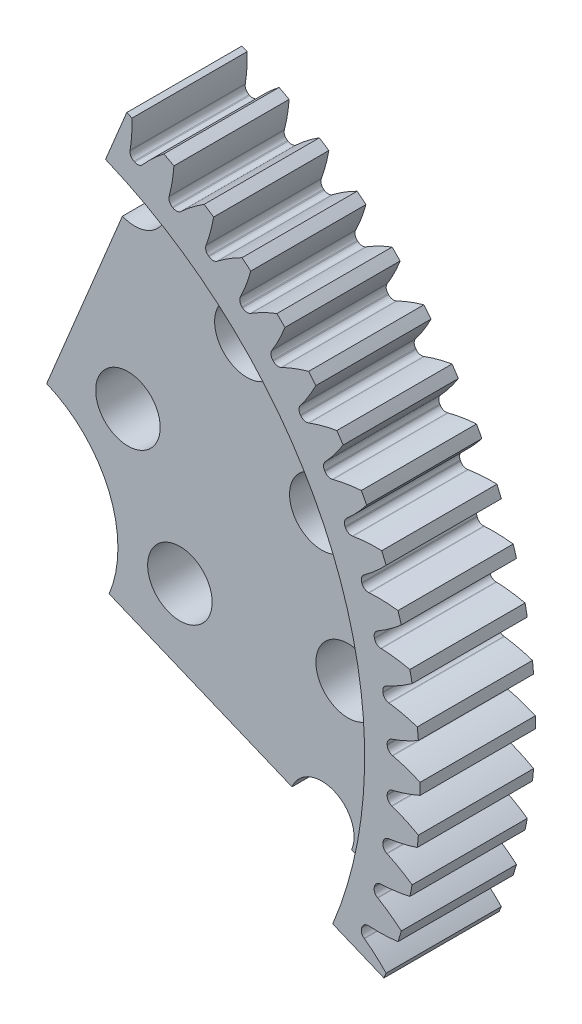
SolidWorks part; units mm, degrees
ref_plane "前视基准面" through (0, 0, 0) normal (0, 0, 1) x (1, 0, 0)
ref_plane "上视基准面" through (0, 0, 0) normal (0, 1, 0) x (1, 0, 0)
ref_plane "右视基准面" through (0, 0, 0) normal (1, 0, 0) x (0, 0, -1)
ref_plane "基准面4" through (0, 0, 0) normal (-0.3827, -0.9239, 0) x (0.9239, -0.3827, 0)
sketch "草图1" plane through (0, 0, 0) normal (-0.3827, -0.9239, 0) x (0.9239, -0.3827, 0)
  line L0 (0, 6.35) -> (0, 0)
  line L1 (0, 0) -> (26.1938, 0)
  line L2 (26.1938, 0) -> (26.1938, 6.35)
  line L3 (26.1938, 6.35) -> (0, 6.35)
  line L4 (0, 6.35) -> (0, 0) construction
revolve "旋转1" add sketch "草图1" angle 90 about L4
sketch "草图2" plane through (0, 0, 0) normal (0, 0, -1) x (-1, 0, 0)
  line L0 (-23.1251, -8.6864) -> (-22.8789, -8.5028)
  line L1 (-23.0797, -7.9415) -> (-23.3866, -7.9557)
  arc A0 (-24.9732, -7.9027) -> (-24.318, -9.7339) centre (0, 0) ccw
  arc A1 (-23.1251, -8.6864) -> (-24.318, -9.7339) centre (-18.0521, -15.6661) ccw
  arc A2 (-22.8789, -8.5028) -> (-23.0797, -7.9415) centre (0, 0) cw
  arc A3 (-24.9732, -7.9027) -> (-23.3866, -7.9557) centre (-23.8956, 0.5798) ccw
extrude "切除-拉伸1" cut sketch "草图2" against normal through all
sketch "草图3" plane through (0, 0, 0) normal (0, 0, -1) x (-1, 0, 0)
  line L0 (-23.8652, -6.3779) -> (-23.6022, -6.2193)
  line L1 (-23.747, -5.641) -> (-24.0537, -5.6251)
  arc A0 (-25.6275, -5.4169) -> (-25.155, -7.3035) centre (0, 0) ccw
  arc A1 (-23.8652, -6.3779) -> (-25.155, -7.3035) centre (-19.5008, -13.8213) ccw
  arc A2 (-23.6022, -6.2193) -> (-23.747, -5.641) centre (0, 0) cw
  arc A3 (-25.6275, -5.4169) -> (-24.0537, -5.6251) centre (-23.7237, 2.9192) ccw
extrude "切除-拉伸2" cut sketch "草图3" against normal through all
sketch "草图4" plane through (0, 0, 0) normal (0, 0, -1) x (-1, 0, 0)
  line L0 (-24.3754, -4.008) -> (-24.0981, -3.8759)
  line L1 (-24.1856, -3.2863) -> (-24.4893, -3.2404)
  arc A0 (-26.0351, -2.8788) -> (-25.7497, -4.8027) centre (0, 0) ccw
  arc A1 (-24.3754, -4.008) -> (-25.7497, -4.8027) centre (-20.7616, -11.8433) ccw
  arc A2 (-24.0981, -3.8759) -> (-24.1856, -3.2863) centre (0, 0) cw
  arc A3 (-26.0351, -2.8788) -> (-24.4893, -3.2404) centre (-23.3233, 5.2304) ccw
extrude "切除-拉伸3" cut sketch "草图4" against normal through all
sketch "草图5" plane through (0, 0, 0) normal (0, 0, -1) x (-1, 0, 0)
  line L0 (-24.6509, -1.5995) -> (-24.362, -1.4952)
  line L1 (-24.3912, -0.8998) -> (-24.689, -0.8244)
  arc A0 (-26.1919, -0.3131) -> (-26.0964, -2.2557) centre (0, 0) ccw
  arc A1 (-24.6509, -1.5995) -> (-26.0964, -2.2557) centre (-21.8225, -9.7513) ccw
  arc A2 (-24.362, -1.4952) -> (-24.3912, -0.8998) centre (0, 0) cw
  arc A3 (-26.1919, -0.3131) -> (-24.689, -0.8244) centre (-22.6984, 7.4913) ccw
extrude "切除-拉伸4" cut sketch "草图5" against normal through all
sketch "草图6" plane through (0, 0, 0) normal (0, 0, -1) x (-1, 0, 0)
  line L0 (-24.689, 0.8244) -> (-24.3912, 0.8998)
  line L1 (-24.362, 1.4952) -> (-24.6509, 1.5995)
  arc A0 (-26.0964, 2.2557) -> (-26.1919, 0.3131) centre (0, 0) ccw
  arc A1 (-24.689, 0.8244) -> (-26.1919, 0.3131) centre (-22.6732, -7.5654) ccw
  arc A2 (-24.3912, 0.8998) -> (-24.362, 1.4952) centre (0, 0) cw
  arc A3 (-26.0964, 2.2557) -> (-24.6509, 1.5995) centre (-21.8548, 9.6801) ccw
extrude "切除-拉伸5" cut sketch "草图6" against normal through all
sketch "草图7" plane through (0, 0, 0) normal (0, 0, -1) x (-1, 0, 0)
  line L0 (-24.4893, 3.2404) -> (-24.1856, 3.2863)
  line L1 (-24.0981, 3.8759) -> (-24.3754, 4.008)
  arc A0 (-25.7497, 4.8027) -> (-26.0351, 2.8788) centre (0, 0) ccw
  arc A1 (-24.4893, 3.2404) -> (-26.0351, 2.8788) centre (-23.3055, -5.3066) ccw
  arc A2 (-24.1856, 3.2863) -> (-24.0981, 3.8759) centre (0, 0) cw
  arc A3 (-25.7497, 4.8027) -> (-24.3754, 4.008) centre (-20.8007, 11.7756) ccw
extrude "切除-拉伸6" cut sketch "草图7" against normal through all
sketch "草图8" plane through (0, 0, 0) normal (0, 0, -1) x (-1, 0, 0)
  line L0 (-24.0537, 5.6251) -> (-23.747, 5.641)
  line L1 (-23.6022, 6.2193) -> (-23.8652, 6.3779)
  arc A0 (-25.155, 7.3035) -> (-25.6275, 5.4169) centre (0, 0) ccw
  arc A1 (-24.0537, 5.6251) -> (-25.6275, 5.4169) centre (-23.7134, -2.9967) ccw
  arc A2 (-23.747, 5.641) -> (-23.6022, 6.2193) centre (0, 0) cw
  arc A3 (-25.155, 7.3035) -> (-23.8652, 6.3779) centre (-19.5464, 13.7577) ccw
extrude "切除-拉伸7" cut sketch "草图8" against normal through all
sketch "草图9" plane through (0, 0, 0) normal (0, 0, -1) x (-1, 0, 0)
  line L0 (-23.3866, 7.9557) -> (-23.0797, 7.9415)
  line L1 (-22.8789, 8.5028) -> (-23.1251, 8.6864)
  arc A0 (-24.318, 9.7339) -> (-24.9732, 7.9027) centre (0, 0) ccw
  arc A1 (-23.3866, 7.9557) -> (-24.9732, 7.9027) centre (-23.893, -0.6579) ccw
  arc A2 (-23.0797, 7.9415) -> (-22.8789, 8.5028) centre (0, 0) cw
  arc A3 (-24.318, 9.7339) -> (-23.1251, 8.6864) centre (-18.1037, 15.6074) ccw
extrude "切除-拉伸8" cut sketch "草图9" against normal through all
sketch "草图10" plane through (0, 0, 0) normal (0, 0, -1) x (-1, 0, 0)
  line L0 (-22.4941, 10.2097) -> (-22.1902, 10.1655)
  line L1 (-21.9353, 10.7043) -> (-22.1623, 10.9112)
  arc A0 (-23.2468, 12.0706) -> (-24.0783, 10.3125) centre (0, 0) ccw
  arc A1 (-22.4941, 10.2097) -> (-24.0783, 10.3125) centre (-23.8424, 1.6872) ccw
  arc A2 (-22.1902, 10.1655) -> (-21.9353, 10.7043) centre (0, 0) cw
  arc A3 (-23.2468, 12.0706) -> (-22.1623, 10.9112) centre (-16.4868, 17.3067) ccw
extrude "切除-拉伸9" cut sketch "草图10" against normal through all
sketch "草图11" plane through (0, 0, 0) normal (0, 0, -1) x (-1, 0, 0)
  line L0 (-21.3851, 12.3653) -> (-21.0869, 12.2915)
  line L1 (-20.7805, 12.8028) -> (-20.9861, 13.031)
  arc A0 (-21.9517, 14.2911) -> (-22.9516, 12.6229) centre (0, 0) ccw
  arc A1 (-21.3851, 12.3653) -> (-22.9516, 12.6229) centre (-23.5622, 4.016) ccw
  arc A2 (-21.0869, 12.2915) -> (-20.7805, 12.8028) centre (0, 0) cw
  arc A3 (-21.9517, 14.2911) -> (-20.9861, 13.031) centre (-14.711, 18.8393) ccw
extrude "切除-拉伸10" cut sketch "草图11" against normal through all
sketch "草图12" plane through (0, 0, 0) normal (0, 0, -1) x (-1, 0, 0)
  line L0 (-20.0701, 14.4019) -> (-19.7806, 14.2992)
  line L1 (-19.4255, 14.778) -> (-19.6078, 15.0252)
  arc A0 (-20.4452, 16.3739) -> (-21.6038, 14.8118) centre (0, 0) ccw
  arc A1 (-20.0701, 14.4019) -> (-21.6038, 14.8118) centre (-23.0551, 6.3062) ccw
  arc A2 (-19.7806, 14.2992) -> (-19.4255, 14.778) centre (0, 0) cw
  arc A3 (-20.4452, 16.3739) -> (-19.6078, 15.0252) centre (-12.7936, 20.1906) ccw
extrude "切除-拉伸11" cut sketch "草图12" against normal through all
sketch "草图13" plane through (0, 0, 0) normal (0, 0, -1) x (-1, 0, 0)
  line L0 (-18.5618, 16.2998) -> (-18.2838, 16.1692)
  line L1 (-17.8835, 16.6109) -> (-18.0407, 16.8748)
  arc A0 (-18.7418, 18.2991) -> (-20.048, 16.858) centre (0, 0) ccw
  arc A1 (-18.5618, 16.2998) -> (-20.048, 16.858) centre (-22.326, 8.5356) ccw
  arc A2 (-18.2838, 16.1692) -> (-17.8835, 16.6109) centre (0, 0) cw
  arc A3 (-18.7418, 18.2991) -> (-18.0407, 16.8748) centre (-10.753, 21.3473) ccw
extrude "切除-拉伸12" cut sketch "草图13" against normal through all
sketch "草图14" plane through (0, 0, 0) normal (0, 0, -1) x (-1, 0, 0)
  line L0 (-16.8748, 18.0407) -> (-16.6109, 17.8835)
  line L1 (-16.1692, 18.2838) -> (-16.2998, 18.5618)
  arc A0 (-16.858, 20.048) -> (-18.2991, 18.7418) centre (0, 0) ccw
  arc A1 (-16.8748, 18.0407) -> (-18.2991, 18.7418) centre (-21.3819, 10.6828) ccw
  arc A2 (-16.6109, 17.8835) -> (-16.1692, 18.2838) centre (0, 0) cw
  arc A3 (-16.858, 20.048) -> (-16.2998, 18.5618) centre (-8.6088, 22.2985) ccw
extrude "切除-拉伸13" cut sketch "草图14" against normal through all
sketch "草图15" plane through (0, 0, 0) normal (0, 0, -1) x (-1, 0, 0)
  line L0 (-15.0252, 19.6078) -> (-14.778, 19.4255)
  line L1 (-14.2992, 19.7806) -> (-14.4019, 20.0701)
  arc A0 (-14.8118, 21.6038) -> (-16.3739, 20.4452) centre (0, 0) ccw
  arc A1 (-15.0252, 19.6078) -> (-16.3739, 20.4452) centre (-20.2318, 12.7272) ccw
  arc A2 (-14.778, 19.4255) -> (-14.2992, 19.7806) centre (0, 0) cw
  arc A3 (-14.8118, 21.6038) -> (-14.4019, 20.0701) centre (-6.3817, 23.035) ccw
extrude "切除-拉伸14" cut sketch "草图15" against normal through all
sketch "草图16" plane through (0, 0, 0) normal (0, 0, -1) x (-1, 0, 0)
  line L0 (-13.031, 20.9861) -> (-12.8028, 20.7805)
  line L1 (-12.2915, 21.0869) -> (-12.3653, 21.3851)
  arc A0 (-12.6229, 22.9516) -> (-14.2911, 21.9517) centre (0, 0) ccw
  arc A1 (-13.031, 20.9861) -> (-14.2911, 21.9517) centre (-18.8869, 14.649) ccw
  arc A2 (-12.8028, 20.7805) -> (-12.2915, 21.0869) centre (0, 0) cw
  arc A3 (-12.6229, 22.9516) -> (-12.3653, 21.3851) centre (-4.0932, 23.5495) ccw
extrude "切除-拉伸15" cut sketch "草图16" against normal through all
sketch "草图17" plane through (0, 0, 0) normal (0, 0, -1) x (-1, 0, 0)
  line L0 (-10.9112, 22.1623) -> (-10.7043, 21.9353)
  line L1 (-10.1655, 22.1902) -> (-10.2097, 22.4941)
  arc A0 (-10.3125, 24.0783) -> (-12.0706, 23.2468) centre (0, 0) ccw
  arc A1 (-10.9112, 22.1623) -> (-12.0706, 23.2468) centre (-17.3601, 16.4297) ccw
  arc A2 (-10.7043, 21.9353) -> (-10.1655, 22.1902) centre (0, 0) cw
  arc A3 (-10.3125, 24.0783) -> (-10.2097, 22.4941) centre (-1.7652, 23.8374) ccw
extrude "切除-拉伸16" cut sketch "草图17" against normal through all
hole_wizard "孔1" positions "草图19" profile "草图18" legacy
sketch "草图19" plane through (0, 0, 6.35) normal (0, 0, 1) x (1, 0, 0)
  point P0 (0, 0)
sketch "草图18" plane through (0, 0, 6.35) normal (1, 0, 0) x (0, -1, 0)
  line L0 (0, 0) -> (0, 6.35)
  line L1 (0, 6.35) -> (6.3627, 6.35)
  line L2 (6.3627, 6.35) -> (6.3627, 3.175)
  line L3 (6.3627, 3.175) -> (23.1378, 3.175)
  line L4 (23.1378, 3.175) -> (23.1378, 0)
  line L5 (23.1378, 0) -> (0, 0)
  line L6 (0, 110) -> (0, -10) construction
  dimension "直径" = 12.7254
  dimension "深度" = 6.35
  dimension "柱坑直径" = 46.2756
  dimension "柱坑深度" = 3.175
hole_wizard "M3 间隙孔1" positions "草图21" profile "草图20" hole size "M3" standard "ANSI Metric"
sketch "草图21" plane through (0, 0, 3.175) normal (0, 0, 1) x (1, 0, 0)
  point P0 (7.2901, 17.5999)
  point P1 (13.4704, 13.4704)
  point P2 (17.5999, 7.2901)
  point P3 (19.05, 0)
  point P4 (6.9148, 6.9148)
  point P5 (9.779, 0)
sketch "草图20" plane through (7.2901, 17.5999, 3.175) normal (1, 0, 0) x (0, -1, 0)
  line L0 (0, 0) -> (0, 3.175)
  line L1 (0, 3.175) -> (1.778, 3.175)
  line L2 (1.778, 3.175) -> (1.778, 0)
  line L5 (1.778, 0) -> (0, 0)
  line L11 (0, -6.35) -> (0, 107.95) construction
  dimension "通孔孔直径" = 3.556
  dimension "通孔孔深度" = 3.175
hole_wizard "M3 间隙孔2" positions "草图23" profile "草图22" hole size "M3" standard "ANSI Metric"
sketch "草图23" plane through (0, 0, 0) normal (0, 0, -1) x (-1, 0, 0)
  point P0 (-17.5999, -7.2901)
sketch "草图22" plane through (17.5999, -7.2901, 0) normal (1, 0, 0) x (0, 1, 0)
  line L0 (0, 0) -> (0, 6.35)
  line L1 (0, 6.35) -> (1.778, 6.35)
  line L2 (1.778, 6.35) -> (1.778, 0)
  line L5 (1.778, 0) -> (0, 0)
  line L11 (0, -6.35) -> (0, 107.95) construction
  dimension "通孔孔直径" = 3.556
  dimension "通孔孔深度" = 6.35
fillet "圆角1" radius 0.371 32 edges at (22.8789, 8.5028, 3.175) (24.362, 1.4952, 3.175) (23.747, -5.641, 3.175) (23.0797, 7.9415, 3.175) (23.0797, -7.9415, 3.175) (16.6109, 17.8835, 3.175) (23.747, 5.641, 3.175) (24.3912, -0.8998, 3.175) (23.6022, -6.2193, 3.175) (16.1692, 18.2838, 3.175) (24.3912, 0.8998, 3.175) (24.362, -1.4952, 3.175) (22.8789, -8.5028, 3.175) (19.7806, 14.2992, 3.175) (20.7805, 12.8028, 3.175) (24.0981, 3.8759, 3.175) (12.8028, 20.7805, 3.175) (19.4255, 14.778, 3.175) (12.2915, 21.0869, 3.175) (24.1856, 3.2863, 3.175) (18.2838, 16.1692, 3.175) (14.778, 19.4255, 3.175) (17.8835, 16.6109, 3.175) (24.1856, -3.2863, 3.175) (10.7043, 21.9353, 3.175) (14.2992, 19.7806, 3.175) (10.1655, 22.1902, 3.175) (24.0981, -3.8759, 3.175) (22.1902, 10.1655, 3.175) (21.0869, 12.2915, 3.175) (21.9353, 10.7043, 3.175) (23.6022, 6.2193, 3.175)
